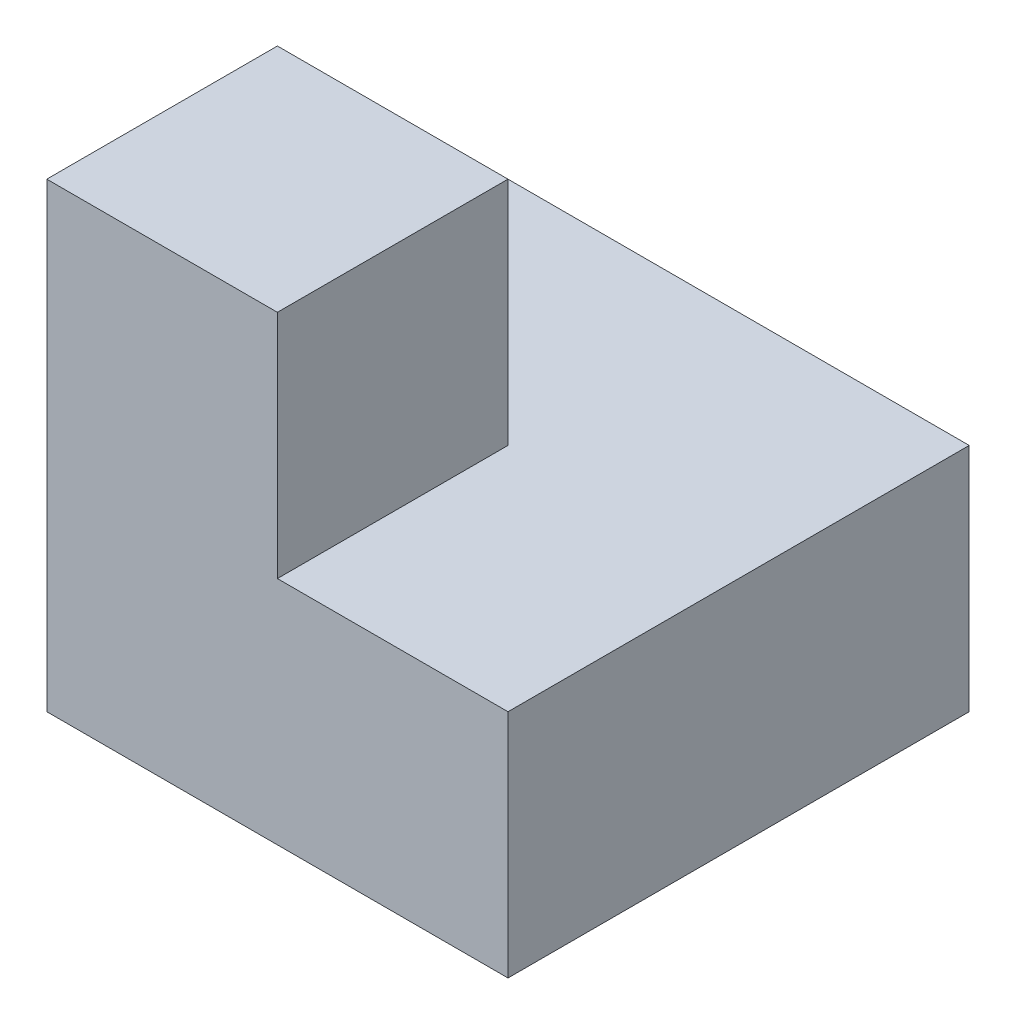
SolidWorks part; units mm, degrees
ref_plane "Front" through (0, 0, 0) normal (0, 0, 1) x (1, 0, 0)
ref_plane "Top" through (0, 0, 0) normal (0, 1, 0) x (1, 0, 0)
ref_plane "Right" through (0, 0, 0) normal (1, 0, 0) x (0, 0, -1)
sketch "Sketch1" plane through (0, 0, 0) normal (0, 1, 0) x (1, 0, 0)
  line L1 (0, 0) -> (4, 0)
  line L2 (0, 0) -> (0, 4)
  line L3 (0, 4) -> (4, 4)
  line L4 (4, 0) -> (4, 4)
  dimension "D1" = 4
  dimension "D2" = 4
extrude "Boss-Extrude1" add sketch "Sketch1" along normal blind 4
sketch "Sketch2" plane through (0, 4, 0) normal (0, 1, 0) x (1, 0, 0)
  line L0 (0, 0) -> (4, 0) construction
  line L5 (0, 2) -> (2, 2)
  line L6 (0, 2) -> (0, 0)
  line L7 (0, 0) -> (2, 0)
  line L8 (2, 2) -> (2, 0)
  line L9 (0, 4) -> (0, 0) construction
  line M1 (0, 4) -> (0, 0)
  line M2 (0, 0) -> (4, 0)
  line M3 (4, 0) -> (4, 4)
  line M4 (4, 4) -> (0, 4)
  dimension "D1" = 0
  dimension "D2" = 0
  dimension "D3" = 2
  dimension "D4" = 2
extrude "Cut-Extrude1" cut sketch "Sketch2" against normal blind 2 contours L8 L7 M4 M1 M2 M3
